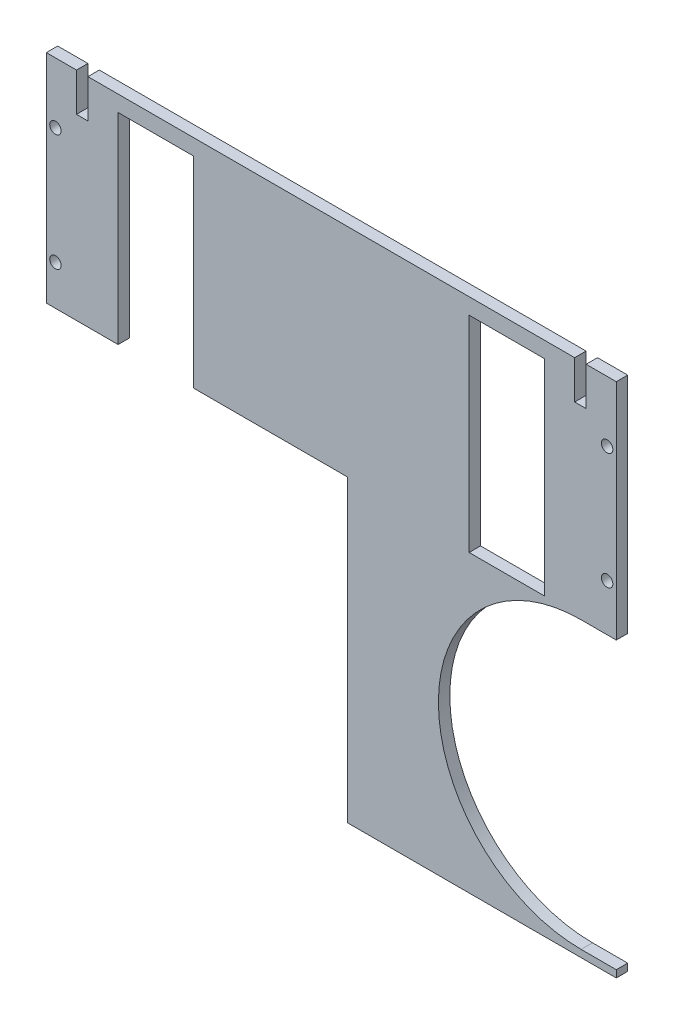
SolidWorks part; units mm, degrees
ref_plane "Front Plane" through (0, 0, 0) normal (0, 0, 1) x (1, 0, 0)
ref_plane "Top Plane" through (0, 0, 0) normal (0, 1, 0) x (1, 0, 0)
ref_plane "Right Plane" through (0, 0, 0) normal (1, 0, 0) x (0, 0, -1)
sketch "Sketch1" plane through (0, 0, 0) normal (0, 0, 1) x (1, 0, 0)
  line L0 (124.8, -69) -> (124.8, -336.4) construction
  line L1 (0, -69) -> (249.6, -69)
  line L2 (0, -69) -> (0, -336.4)
  line L3 (0, -336.4) -> (249.6, -336.4)
  line L4 (249.6, -69) -> (249.6, -336.4)
  line L9 (185.16, -76) -> (218.16, -76)
  line L10 (185.16, -76) -> (185.16, -166)
  line L11 (185.16, -166) -> (218.16, -166)
  line L12 (218.16, -76) -> (218.16, -166)
  line L13 (249.6, -69) -> (0, -69) construction
  line L15 (249.6, -167) -> (249.6, -69) construction
  line L21 (0, -289) -> (0, -336.4) construction
  line L25 (249.6, -336.4) -> (0, -336.4) construction
  line L52 (204.16, -76) -> (204.16, -166) construction
  line L53 (194.16, -76) -> (214.16, -76) construction
  line L54 (194.16, -76) -> (194.16, -166) construction
  line L55 (194.16, -166) -> (214.16, -166) construction
  line L56 (214.16, -76) -> (214.16, -166) construction
  line L102 (245.6, -95.5) -> (245.6, -146.5) construction
  line L103 (218.16, -121) -> (245.6, -121) construction
  line L134 (31.44, -121) -> (4, -121) construction
  line L135 (4, -95.5) -> (4, -146.5) construction
  line L139 (35.44, -76) -> (35.44, -166) construction
  line L140 (55.44, -166) -> (35.44, -166) construction
  line L141 (55.44, -76) -> (55.44, -166) construction
  line L142 (55.44, -76) -> (35.44, -76) construction
  line L143 (45.44, -76) -> (45.44, -166) construction
  line L154 (31.44, -76) -> (31.44, -166)
  line L155 (64.44, -166) -> (31.44, -166)
  line L156 (64.44, -76) -> (64.44, -166)
  line L157 (64.44, -76) -> (31.44, -76)
  circle A84 centre (245.6, -95.5) radius 2.5
  circle A85 centre (245.6, -146.5) radius 2.5
  circle A236 centre (4, -146.5) radius 2.5
  circle A237 centre (4, -95.5) radius 2.5
  dimension "D5" = 20
  dimension "D15" = 5
  dimension "D16" = 5
  dimension "D3" = 4
  dimension "D4" = 90
  dimension "D6" = 90
  dimension "D7" = 9
  dimension "D8" = 7
  dimension "D14" = 89.36
  dimension "D17" = 25.5
  dimension "D18" = 4
extrude "Boss-Extrude1" add sketch "Sketch1" along normal blind 5
sketch "Sketch2" plane through (0, 0, 5) normal (0, 0, 1) x (1, 0, 0)
  line L0 (-0.8818, -199.1061) -> (0.8939, -68.1182) construction
  line L1 (377.0835, -204.2298) -> (378.8591, -73.2419) construction
  line L2 (-0.8818, -199.1061) -> (377.0835, -204.2298) construction
  line L3 (14.5032, -15.3834) -> (11.5694, -19.4322) construction
  line L4 (11.5694, -19.4322) -> (65.6935, -58.6513) construction
  line L5 (75.64, -59.684) -> (14.5032, -15.3834) construction
  line L6 (0.8939, -68.1182) -> (378.8591, -73.2419) construction
  line L7 (0.8532, -71.1179) -> (378.8185, -76.2416) construction
  line L8 (-0.8412, -196.1064) -> (377.1241, -201.2301) construction
  line L9 (14.5032, -15.3834) -> (17.4371, -11.3347) construction
  line L10 (17.4371, -11.3347) -> (71.5611, -50.5537) construction
  line L11 (252.1356, -199.5358) -> (253.8299, -74.5473) construction
  line L12 (127.9943, -135.3472) -> (252.9828, -137.0415) construction
  line L13 (127.1471, -197.8414) -> (128.8414, -72.8529) construction
  line L14 (249.6, -69) -> (0, -69) construction
  line L15 (0, -69) -> (0, -336.4) construction
  circle A0 centre (65.5, -134.5) radius 62.5 construction
  circle A1 centre (315.477, -137.8887) radius 62.5 construction
  circle A2 centre (65.5, -134.5) radius 65.5 construction
  circle A3 centre (190.4885, -136.1943) radius 62.5 construction
  circle A4 centre (75.64, -59.684) radius 75.5 construction
  circle A5 centre (75.64, -59.684) radius 2.5 construction
  circle A6 centre (55.3961, -45.015) radius 1.5 construction
  arc A7 (65.6935, -58.6513) -> (71.5611, -50.5537) centre (75.64, -59.684) ccw construction
  dimension "D1" = 125
  dimension "D2" = 125
  dimension "D3" = 5
  dimension "D6" = 3
  dimension "D7" = 10
  dimension "D10" = 125
  dimension "D8" = 3
  dimension "D4" = 5
  dimension "D5" = 25
  dimension "D9" = 5
ref_plane "Plane1"
sketch "Sketch6" plane through (0, 0, 5) normal (0, 0, 1) x (1, 0, 0)
  line L4 (132, -295.148) -> (249.6, -295.148)
  line L5 (0, -336.4) -> (249.6, -336.4)
  line L7 (0, -227) -> (0, -164)
  line L8 (0, -164) -> (132, -164)
  line L9 (0, -167) -> (0, -289) construction
  line L10 (234.206, -292) -> (296.706, -292)
  line L11 (296.706, -292) -> (296.706, -167)
  line L12 (296.706, -167) -> (234.206, -167)
  line L13 (0, -336.4) -> (249.6, -336.4) construction
  line L14 (0, -336.4) -> (0, -227)
  line L15 (132, -295.148) -> (132, -164)
  line L17 (0, -69) -> (0, -336.4) construction
  line L18 (0, -167) -> (249.6, -167) construction
  line L19 (247.6, -295.148) -> (237.6, -295.148) construction
  line L21 (249.6, -295.148) -> (249.6, -336.4)
  line L23 (249.6, -336.4) -> (249.6, -69) construction
  line L25 (127, -167) -> (127, -419.4) construction
  arc A2 (234.206, -167) -> (234.206, -292) centre (234.206, -229.5) ccw
  arc A3 (234.206, -167) -> (195.5325, -278.598) centre (234.206, -229.5) ccw construction
  point P12 (249.6, -241.148)
  dimension "D1" = 3
  dimension "D3" = 5
extrude "Cut-Extrude4" cut sketch "Sketch6" against normal through all
sketch "Sketch7" plane through (0, 0, 5) normal (0, 0, 1) x (1, 0, 0)
  line L0 (124.8, 45.2798) -> (124.8, -137.1886) construction
  line L17 (0, -163) -> (249.6, -163) construction
  line L18 (13.22, -20.8123) -> (18.22, -20.8123)
  line L19 (13.22, -20.8123) -> (13.22, -40.8123)
  line L20 (249.6, -167) -> (249.6, -69) construction
  line L21 (218.16, -166) -> (218.16, -76) construction
  line L23 (13.22, -40.8123) -> (18.22, -40.8123)
  line L24 (18.22, -20.8123) -> (18.22, -40.8123)
  line L25 (231.38, -20.8123) -> (236.38, -20.8123)
  line L26 (231.38, -20.8123) -> (231.38, -40.8123)
  line L27 (231.38, -40.8123) -> (236.38, -40.8123)
  line L28 (236.38, -20.8123) -> (236.38, -40.8123)
  line L29 (13.22, -60.8123) -> (18.22, -60.8123)
  line L30 (13.22, -60.8123) -> (13.22, -85.8123)
  line L31 (13.22, -85.8123) -> (18.22, -85.8123)
  line L32 (18.22, -60.8123) -> (18.22, -85.8123)
  line L33 (231.38, -60.8123) -> (236.38, -60.8123)
  line L34 (231.38, -60.8123) -> (231.38, -85.8123)
  line L35 (231.38, -85.8123) -> (236.38, -85.8123)
  line L36 (236.38, -60.8123) -> (236.38, -85.8123)
  line L37 (15.72, -20.8123) -> (15.72, -102.3359) construction
  line L38 (233.88, -20.8123) -> (233.88, -163) construction
  line L39 (0, -69) -> (0, -164) construction
  line L40 (249.6, -167) -> (249.6, -69) construction
  dimension "D1" = 5
  dimension "D2" = 20
  dimension "D3" = 5
  dimension "D4" = 20
  dimension "D5" = 5
  dimension "D6" = 25
  dimension "D7" = 5
  dimension "D8" = 25
  dimension "D9" = 20
  dimension "D10" = 20
extrude "Cut-Extrude5" cut sketch "Sketch7" against normal through all
